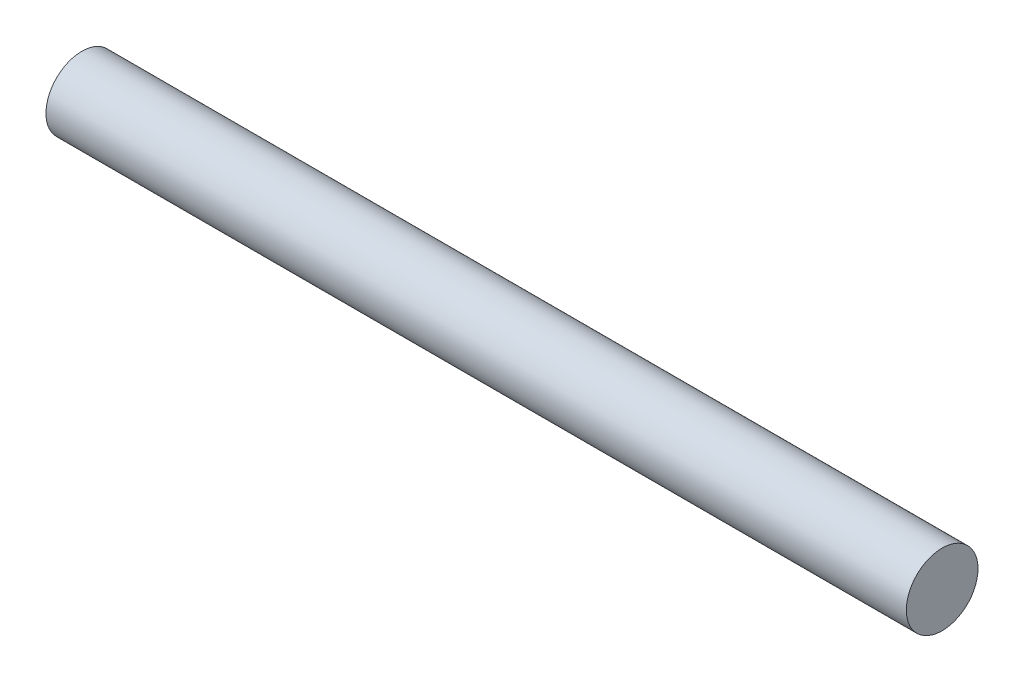
SolidWorks part; units mm, degrees
material "6061-T6 (SS)"
ref_plane "Front Plane" through (0, 0, 0) normal (0, 0, 1) x (1, 0, 0)
ref_plane "Top Plane" through (0, 0, 0) normal (0, 1, 0) x (1, 0, 0)
ref_plane "Right Plane" through (0, 0, 0) normal (1, 0, 0) x (0, 0, -1)
sketch "Sketch1" plane through (0, 0, 0) normal (1, 0, 0) x (0, 0, -1)
  circle A0 centre (0, 0) radius 1.5875
  dimension "D1" = 3.175
extrude "Boss-Extrude1" add sketch "Sketch1" along normal blind 38.1
